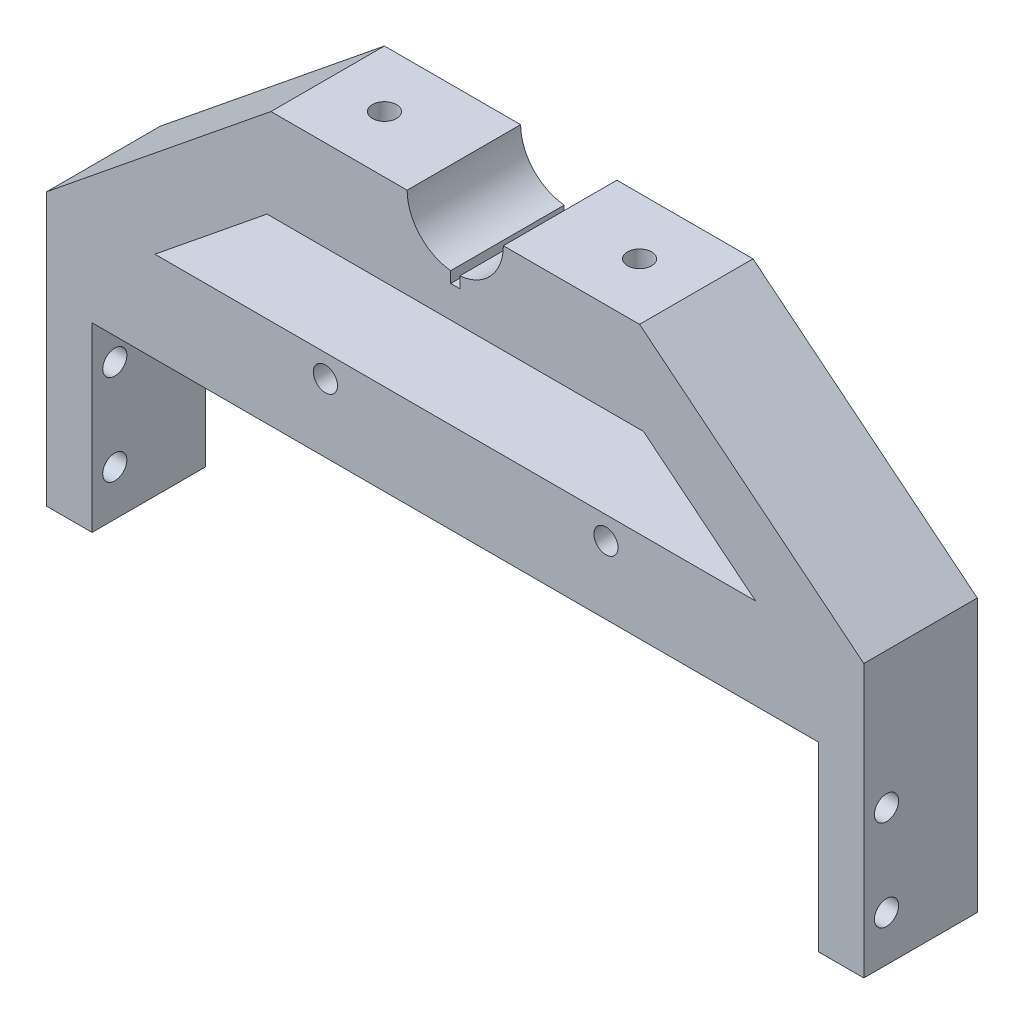
SolidWorks part; units mm, degrees
ref_plane "Front Plane" through (0, 0, 0) normal (0, 0, 1) x (1, 0, 0)
ref_plane "Top Plane" through (0, 0, 0) normal (0, 1, 0) x (1, 0, 0)
ref_plane "Right Plane" through (0, 0, 0) normal (1, 0, 0) x (0, 0, -1)
sketch "Sketch2" plane through (0, 0, 0) normal (0, 0, 1) x (1, 0, 0)
  line L0 (254, 0) -> (266.7, 0)
  line L4 (266.7, 0) -> (266.7, 101.6)
  line L9 (50.8, 0) -> (38.1, 0)
  line L10 (38.1, 0) -> (38.1, 101.6)
  line L12 (38.1, 101.6) -> (100.838, 152.4)
  line L13 (266.7, 101.6) -> (203.962, 152.4)
  line L14 (100.838, 152.4) -> (138.938, 152.4)
  line L15 (165.862, 152.4) -> (203.962, 152.4)
  line L16 (50.8, 0) -> (50.8, 76.2)
  line L17 (50.8, 76.2) -> (254, 76.2)
  line L18 (254, 76.2) -> (254, 0)
  arc A3 (138.938, 152.4) -> (165.862, 152.4) centre (152.4, 152.4) ccw
  dimension "D3" = 12.7
  dimension "D7" = 13.462
  dimension "D2" = 12.7
  dimension "D4" = 228.6
  dimension "D5" = 38.1
  dimension "D8" = 114.3
  dimension "D9" = 38.1
  dimension "D10" = 101.6
  dimension "D11" = 50.8
  dimension "D12" = 76.2
  dimension "D13" = 101.6
  dimension "D14" = 203.2
extrude "Boss-Extrude1" add sketch "Sketch2" along normal blind 50.8
sketch "Sketch3" plane through (38.1, 0, 0) normal (-1, 0, 0) x (0, 0, 1)
  line L2 (50.8, 0) -> (0, 0) construction
  circle A0 centre (25.4, 63.5) radius 3.3782
  circle A1 centre (25.4, 38.1) radius 3.3782
  dimension "D1" = 6.7564
  dimension "D2" = 6.7564
  dimension "D3" = 38.1
  dimension "D4" = 25.4
extrude "Cut-Extrude1" cut sketch "Sketch3" against normal blind 25.4
sketch "Sketch4" plane through (266.7, 0, 0) normal (1, 0, 0) x (0, 0, -1)
  line L1 (-50.8, 0) -> (0, 0) construction
  circle A0 centre (-25.4, 63.5) radius 3.3782
  circle A1 centre (-25.4, 38.1) radius 3.3782
  dimension "D1" = 6.7564
  dimension "D2" = 6.7564
  dimension "D5" = 38.1
  dimension "D6" = 63.5
extrude "Cut-Extrude2" cut sketch "Sketch4" against normal blind 25.4
sketch "Sketch7" plane through (0, 0, 50.8) normal (0, 0, 1) x (1, 0, 0)
  line L1 (12.1672, -21.2745) -> (291.9081, -21.2745)
  line L2 (12.1672, -21.2745) -> (12.1672, 173.6745)
  line L3 (12.1672, 173.6745) -> (291.9081, 173.6745)
  line L4 (291.9081, -21.2745) -> (291.9081, 173.6745)
extrude "Cut-Extrude5" cut sketch "Sketch7" against normal blind 19.05
sketch "Sketch8" plane through (0, 0, 31.75) normal (0, 0, 1) x (1, 0, 0)
  line L0 (38.1, 0) -> (38.1, 101.6) construction
  line L1 (38.1, 25.4) -> (266.7, 25.4)
  line L2 (38.1, 25.4) -> (38.1, 0)
  line L3 (38.1, 0) -> (266.7, 0)
  line L4 (266.7, 25.4) -> (266.7, 0)
  dimension "D1" = 25.4
extrude "Cut-Extrude6" cut sketch "Sketch8" against normal blind 39.37
sketch "Sketch9" plane through (0, 152.4, 0) normal (0, 1, 0) x (1, 0, 0)
  line L1 (138.938, 0) -> (100.838, 0) construction
  line L2 (203.962, 0) -> (165.862, 0) construction
  line L4 (100.838, -31.75) -> (100.838, 0) construction
  line L5 (203.962, -31.75) -> (203.962, 0) construction
  circle A0 centre (116.713, -15.875) radius 3.3782
  circle A1 centre (188.087, -15.875) radius 3.3782
  dimension "D1" = 6.7564
  dimension "D2" = 6.7564
  dimension "D3" = 15.875
  dimension "D4" = 15.875
  dimension "D5" = 15.875
  dimension "D6" = 15.875
extrude "Cut-Extrude7" cut sketch "Sketch9" against normal blind 27.94
sketch "Sketch10" plane through (0, 0, 31.75) normal (0, 0, 1) x (1, 0, 0)
  line L7 (68.3723, 101.6) -> (99.7413, 127)
  line L8 (99.7413, 127) -> (205.0587, 127)
  line L9 (68.3723, 101.6) -> (236.4277, 101.6)
  line L10 (38.1, 101.6) -> (100.838, 152.4) construction
  line L11 (205.0587, 127) -> (236.4277, 101.6)
  line L12 (203.962, 152.4) -> (266.7, 101.6) construction
  dimension "D1" = 25.4
  dimension "D2" = 19.05
  dimension "D3" = 19.05
extrude "Cut-Extrude8" cut sketch "Sketch10" against normal blind 40.64
sketch "Sketch12" plane through (0, 152.4, 0) normal (0, 1, 0) x (1, 0, 0)
  line L0 (152.4, -31.75) -> (152.4, 0)
  line L1 (138.938, -31.75) -> (165.862, -31.75) construction
  line L2 (165.862, 0) -> (138.938, 0) construction
  line L3 (152.4, 0) -> (153.67, 0)
  line L4 (153.67, 0) -> (153.67, -31.75)
  line L5 (153.67, -31.75) -> (151.13, -31.75)
  line L6 (151.13, -31.75) -> (151.13, 0)
  line L7 (151.13, 0) -> (152.4, 0)
  dimension "D1" = 1.27
  dimension "D2" = 1.27
extrude "Cut-Extrude9" cut sketch "Sketch12" against normal blind 16.51 contours L5 L4 L3 L0 | L7 L6 L5 L0
sketch "Sketch13" plane through (0, 0, 31.75) normal (0, 0, 1) x (1, 0, 0)
  line L1 (68.3723, 101.6) -> (236.4277, 101.6) construction
  line L2 (38.1, 25.4) -> (38.1, 101.6) construction
  circle A0 centre (116.078, 95.25) radius 3.3782
  circle A1 centre (194.564, 95.25) radius 3.3782
  dimension "D1" = 6.7564
  dimension "D2" = 6.7564
  dimension "D3" = 6.35
  dimension "D4" = 6.35
  dimension "D5" = 77.978
  dimension "D6" = 156.464
extrude "Cut-Extrude10" cut sketch "Sketch13" against normal up to next
